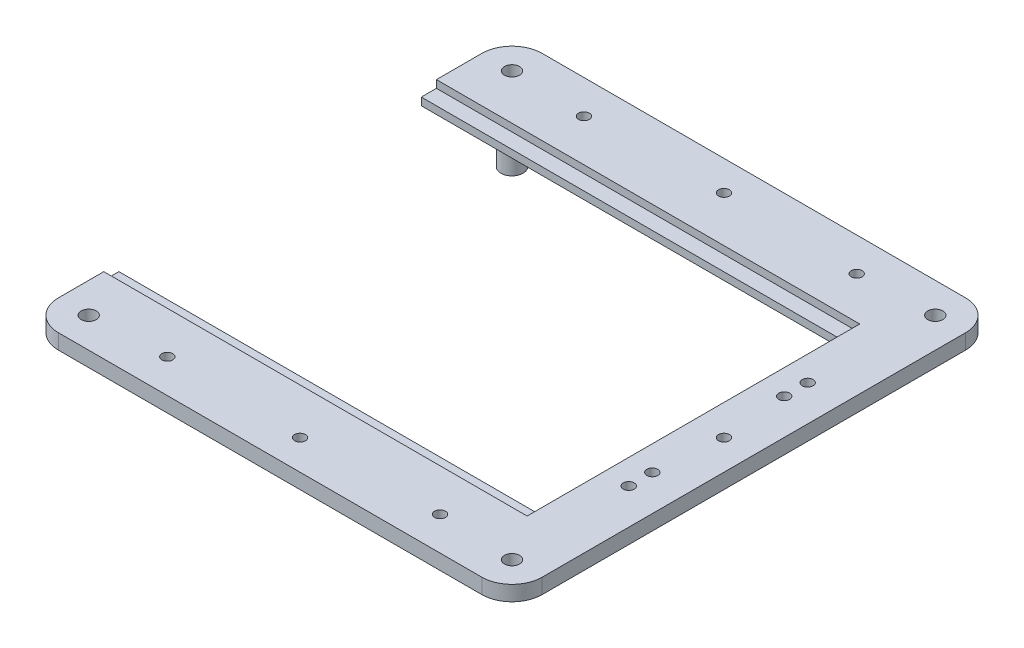
SolidWorks part; units mm, degrees
ref_plane "Front Plane" through (0, 0, 0) normal (0, 0, 1) x (1, 0, 0)
ref_plane "Top Plane" through (0, 0, 0) normal (0, 1, 0) x (1, 0, 0)
ref_plane "Right Plane" through (0, 0, 0) normal (1, 0, 0) x (0, 0, -1)
sketch "Sketch1" plane through (0, 0, 0) normal (0, 1, 0) x (1, 0, 0)
  line L0 (0, 0) -> (0, 25.4)
  line L1 (12.7, 38.1) -> (190.5, 38.1)
  line L2 (203.2, 25.4) -> (203.2, -152.4)
  line L3 (190.5, -165.1) -> (12.7, -165.1)
  line L4 (0, -152.4) -> (0, -127)
  line L5 (0, -127) -> (177.8, -127)
  line L6 (177.8, -127) -> (177.8, 0)
  line L7 (177.8, 0) -> (0, 0)
  arc A0 (12.7, -165.1) -> (0, -152.4) centre (12.7, -152.4) cw
  arc A1 (203.2, -152.4) -> (190.5, -165.1) centre (190.5, -152.4) cw
  arc A2 (190.5, 38.1) -> (203.2, 25.4) centre (190.5, 25.4) cw
  arc A3 (0, 25.4) -> (12.7, 38.1) centre (12.7, 25.4) cw
  point P13 (203.2, -165.1)
  point P16 (203.2, 38.1)
  point P19 (0, 38.1)
  dimension "D6" = 12.7
  dimension "D1" = 203.2
  dimension "D2" = 38.1
  dimension "D3" = 203.2
  dimension "D4" = 177.8
  dimension "D5" = 127
extrude "Boss-Extrude2" add sketch "Sketch1" along normal blind 6.35
sketch "Sketch2" plane through (0, 6.35, 0) normal (0, 1, 0) x (1, 0, 0)
  circle A0 centre (12.7, 25.4) radius 3.175
  circle A1 centre (190.5, 25.4) radius 3.175
  circle A2 centre (190.5, -152.4) radius 3.175
  circle A3 centre (12.7, -152.4) radius 3.175
  arc A4 (12.7, 38.1) -> (0, 25.4) centre (12.7, 25.4) ccw construction
  dimension "D1" = 6.35
extrude "Cut-Extrude1" cut sketch "Sketch2" against normal through all
sketch "Sketch5" plane through (0, 0, 0) normal (0, -1, 0) x (1, 0, 0)
  line L0 (0, 127) -> (0, 152.4) construction
  line L1 (12.7, 165.1) -> (190.5, 165.1) construction
  line L2 (203.2, 152.4) -> (203.2, -25.4) construction
  line L4 (203.2, 63.5) -> (0, 63.5) construction
  circle A0 centre (28.575, 136.525) radius 4.6625
  circle A1 centre (174.625, 136.525) radius 4.6625
  circle A4 centre (174.625, -9.525) radius 4.6625
  circle A5 centre (28.575, -9.525) radius 4.6625
  dimension "D1" = 28.575
  dimension "D2" = 28.575
  dimension "D3" = 9.325
  dimension "D4" = 28.575
  dimension "D5" = 28.575
extrude "Boss-Extrude3" add sketch "Sketch5" along normal blind 12.7
sketch "Sketch6" plane through (0, 6.35, 0) normal (0, 1, 0) x (1, 0, 0)
  line L0 (0, -127) -> (0, -152.4) construction
  line L1 (177.8, -127) -> (0, -127)
  line L2 (177.8, -127) -> (177.8, -133.35)
  line L3 (177.8, -133.35) -> (0, -133.35)
  line L4 (0, -127) -> (0, -133.35)
  line L5 (203.2, -63.5) -> (0, -63.5) construction
  line L6 (203.2, -152.4) -> (203.2, 25.4) construction
  line L7 (0, 0) -> (0, 6.35)
  line L8 (177.8, 6.35) -> (0, 6.35)
  line L9 (177.8, 0) -> (177.8, 6.35)
  line L10 (177.8, 0) -> (0, 0)
  dimension "D1" = 6.35
extrude "Cut-Extrude2" cut sketch "Sketch6" against normal blind 3.175
sketch "Sketch7" plane through (0, 6.35, 0) normal (0, 1, 0) x (1, 0, 0)
  line L0 (188.214, -28.194) -> (188.214, -33.528) construction
  line L1 (188.214, -38.1) -> (188.214, -88.9) construction
  line L2 (188.214, -93.472) -> (188.214, -98.806) construction
  line L3 (188.214, -23.622) -> (188.214, 38.1) construction
  line L4 (190.5, 38.1) -> (12.7, 38.1) construction
  line L5 (188.214, -103.378) -> (188.214, -165.1) construction
  line L6 (12.7, -165.1) -> (190.5, -165.1) construction
  line L7 (185.928, -25.908) -> (177.8, -25.908) construction
  line L8 (177.8, 6.35) -> (177.8, -133.35) construction
  circle A0 centre (188.214, -101.092) radius 2.286
  circle A1 centre (188.214, -91.186) radius 2.286
  circle A2 centre (188.214, -35.814) radius 2.286
  circle A3 centre (188.214, -25.908) radius 2.286
  dimension "D1" = 4.572
  dimension "D2" = 5.334
  dimension "D3" = 5.334
  dimension "D4" = 50.8
  dimension "D5" = 8.128
extrude "Cut-Extrude3" cut sketch "Sketch7" against normal blind 12.7
sketch "Sketch8" plane through (0, 6.35, 0) normal (0, 1, 0) x (1, 0, 0)
  line L0 (12.7, -152.4) -> (190.5, 25.4) construction
  line L1 (12.7, 25.4) -> (190.5, -152.4) construction
  line L2 (190.5, 38.1) -> (12.7, 38.1) construction
  circle A0 centre (101.6, 25.527) radius 2.286
  circle A1 centre (190.627, -63.5) radius 2.286
  circle A2 centre (101.6, -152.527) radius 2.286
  circle A4 centre (12.573, -63.5) radius 2.286 [skipped]
  point P12 (101.6, 38.1)
  point P13 (101.6, -63.5)
  dimension "D3" = 4.572
  dimension "D2" = 12.573
  dimension "D1" = 4
extrude "Cut-Extrude4" cut sketch "Sketch8" against normal through all
sketch "Sketch9" plane through (0, 6.35, 0) normal (0, 1, 0) x (1, 0, 0)
  line L0 (0, 25.4) -> (0, 6.35) construction
  line L1 (203.2, -152.4) -> (203.2, 25.4) construction
  line L2 (190.5, 38.1) -> (12.7, 38.1) construction
  line L3 (12.7, -165.1) -> (190.5, -165.1) construction
  circle A0 centre (44.321, 24) radius 2.286
  circle A1 centre (44.321, -151) radius 2.286
  circle A2 centre (158.879, -151) radius 2.286
  circle A3 centre (158.879, 24) radius 2.286
  point P8 (0, 0)
  point P9 (0, 0)
  point P10 (0, 0)
  dimension "D1" = 4.572
  dimension "D2" = 44.321
  dimension "D3" = 44.321
  dimension "D4" = 14.1
  dimension "D5" = 14.1
extrude "Cut-Extrude5" cut sketch "Sketch9" against normal through all
